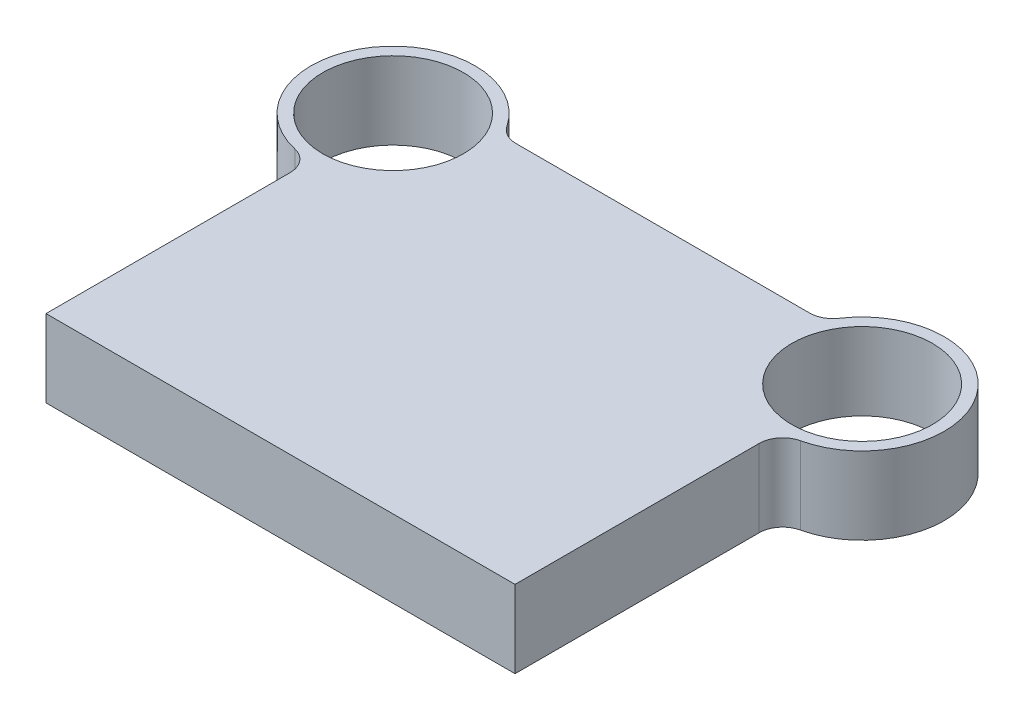
SolidWorks part; units mm, degrees
ref_plane "Front Plane" through (0, 0, 0) normal (0, 0, 1) x (1, 0, 0)
ref_plane "Top Plane" through (0, 0, 0) normal (0, 1, 0) x (1, 0, 0)
ref_plane "Right Plane" through (0, 0, 0) normal (1, 0, 0) x (0, 0, -1)
sketch "Sketch1" plane through (0, 0, 0) normal (0, 1, 0) x (1, 0, 0)
  line L0 (100, 0) -> (-100, 0)
  line L1 (-100, 0) -> (-100, 113)
  line L2 (0, 0) -> (0, 163) construction
  line L3 (68.3772, 163) -> (-68.3772, 163)
  line L4 (100, 0) -> (100, 113)
  arc A0 (-68.3772, 163) -> (-100, 113) centre (-100, 148) ccw
  circle A1 centre (-100, 148) radius 30
  circle A2 centre (100, 148) radius 30
  arc A3 (68.3772, 163) -> (100, 113) centre (100, 148) cw
  point P7 (-121.6072, 163.3679)
  point P10 (-140.316, 130.9633)
  point P11 (-85.9554, 174.7269)
  point P12 (-124.9481, 148)
  dimension "D3" = 70
  dimension "D4" = 60
  dimension "D1" = 148
  dimension "D2" = 163
  dimension "D5" = 200
  dimension "D6" = 200
extrude "Boss-Extrude1" add sketch "Sketch1" along normal blind 33
fillet "Fillet1" radius 10 4 edges at (100, 16.5, -113) (68.3772, 16.5, -163) (-68.3772, 16.5, -163) (-100, 16.5, -113)
